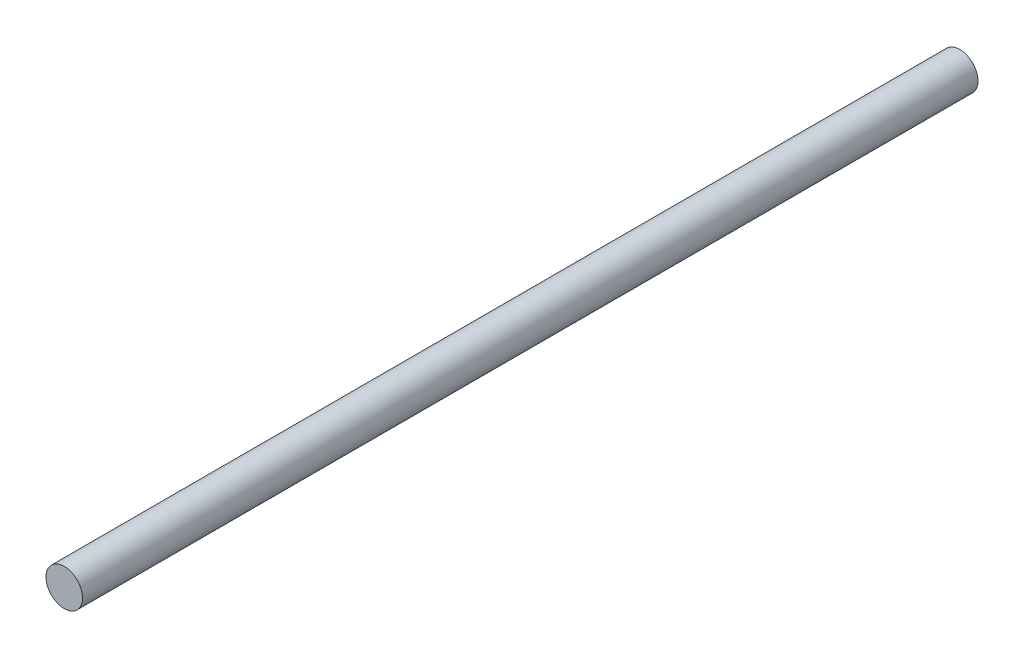
SolidWorks part; units mm, degrees
ref_plane "前视基准面" through (0, 0, 0) normal (0, 0, 1) x (1, 0, 0)
ref_plane "上视基准面" through (0, 0, 0) normal (0, 1, 0) x (1, 0, 0)
ref_plane "右视基准面" through (0, 0, 0) normal (1, 0, 0) x (0, 0, -1)
other "Configuration Table"
sketch "草图1" plane through (0, 0, 0) normal (0, 0, 1) x (1, 0, 0)
  circle A0 centre (0, 0) radius 4
  dimension "D1" = 8
extrude "凸台-拉伸1" add sketch "草图1" along normal blind 196
